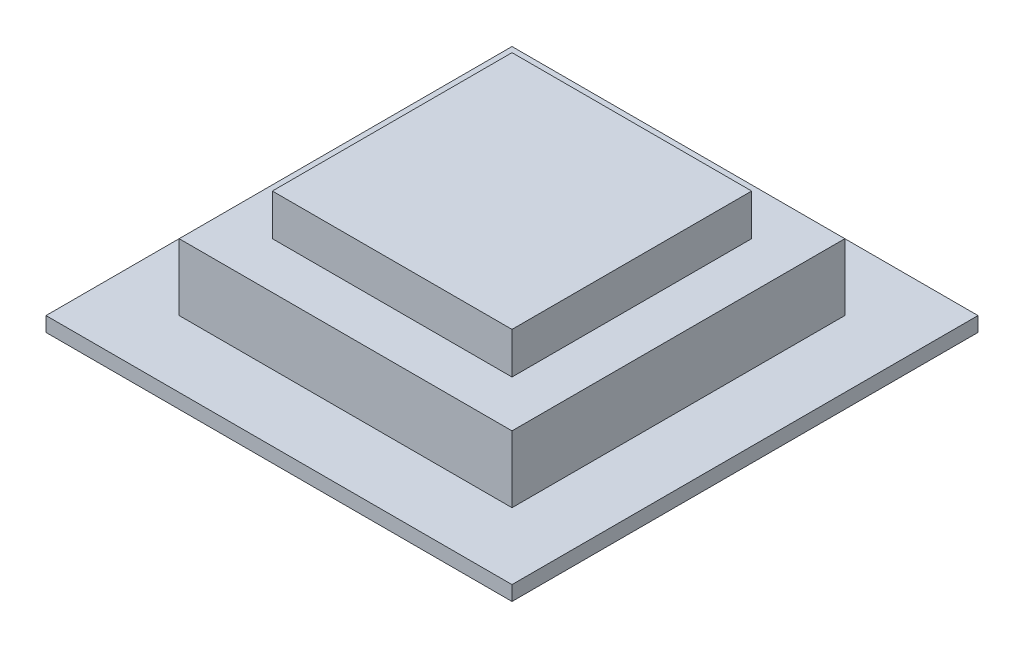
SolidWorks part; units mm, degrees
ref_plane "Front Plane" through (0, 0, 0) normal (0, 0, 1) x (1, 0, 0)
ref_plane "Top Plane" through (0, 0, 0) normal (0, 1, 0) x (1, 0, 0)
ref_plane "Right Plane" through (0, 0, 0) normal (1, 0, 0) x (0, 0, -1)
sketch "Sketch1" plane through (0, 0, 0) normal (0, 1, 0) x (1, 0, 0)
  line L1 (-17.5, -17.5) -> (17.5, -17.5)
  line L2 (-17.5, -17.5) -> (-17.5, 17.5)
  line L3 (-17.5, 17.5) -> (17.5, 17.5)
  line L4 (17.5, -17.5) -> (17.5, 17.5)
  line L5 (-17.5, -17.5) -> (17.5, 17.5) construction
  line L6 (-17.5, 17.5) -> (17.5, -17.5) construction
  point P0 (0, 0)
  dimension "D1" = 35
extrude "Boss-Extrude1" add sketch "Sketch1" along normal blind 1.1
sketch "Sketch2" plane through (0, 1.1, 0) normal (0, 1, 0) x (1, 0, 0)
  line L1 (-12.5, -12.5) -> (12.5, -12.5)
  line L2 (-12.5, -12.5) -> (-12.5, 12.5)
  line L3 (-12.5, 12.5) -> (12.5, 12.5)
  line L4 (12.5, -12.5) -> (12.5, 12.5)
  line L5 (-12.5, -12.5) -> (12.5, 12.5) construction
  line L6 (-12.5, 12.5) -> (12.5, -12.5) construction
  point P0 (0, 0)
  dimension "D1" = 25
extrude "Boss-Extrude2" add sketch "Sketch2" along normal blind 5
sketch "Sketch3" plane through (0, 6.1, 0) normal (0, 1, 0) x (1, 0, 0)
  line L1 (-9, -9) -> (9, -9)
  line L2 (-9, -9) -> (-9, 9)
  line L3 (-9, 9) -> (9, 9)
  line L4 (9, -9) -> (9, 9)
  line L5 (-9, -9) -> (9, 9) construction
  line L6 (-9, 9) -> (9, -9) construction
  point P0 (0, 0)
  dimension "D1" = 18
extrude "Boss-Extrude6" add sketch "Sketch3" along normal blind 3.1 contours L1 L4 L3 L2
